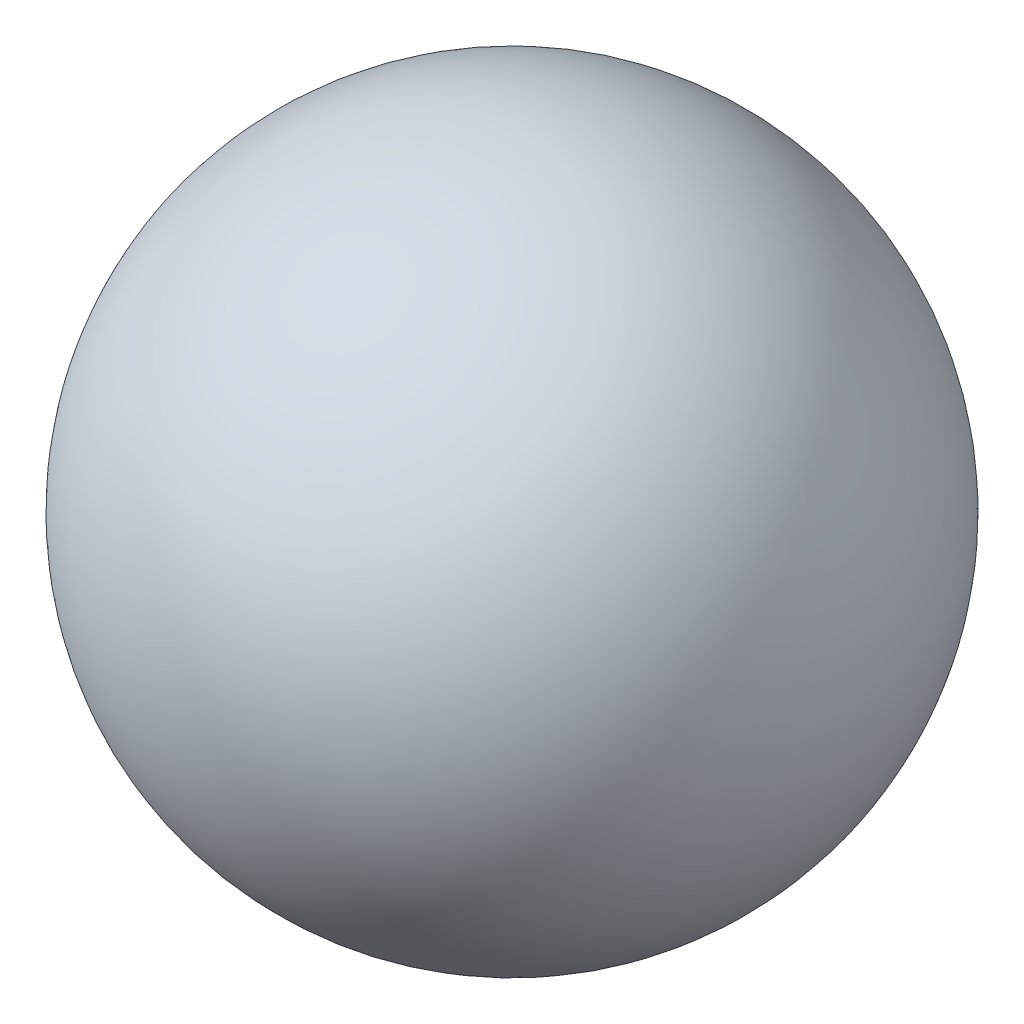
SolidWorks part; units mm, degrees
material "Plain Carbon Steel"
ref_plane "Front Plane" through (0, 0, 0) normal (0, 0, 1) x (1, 0, 0)
ref_plane "Top Plane" through (0, 0, 0) normal (0, 1, 0) x (1, 0, 0)
ref_plane "Right Plane" through (0, 0, 0) normal (1, 0, 0) x (0, 0, -1)
sketch "Sketch2" plane through (0, 0, 0) normal (0, 1, 0) x (1, 0, 0)
  line L0 (-1.8688, 0) -> (2.8366, 0) construction
  line L1 (-2.3813, 0) -> (2.3813, 0)
  arc A0 (2.3813, 0) -> (-2.3813, 0) centre (0, 0) ccw
  dimension "D1" = 4.7625
revolve "Revolve5" add sketch "Sketch2" angle 360 about L0
